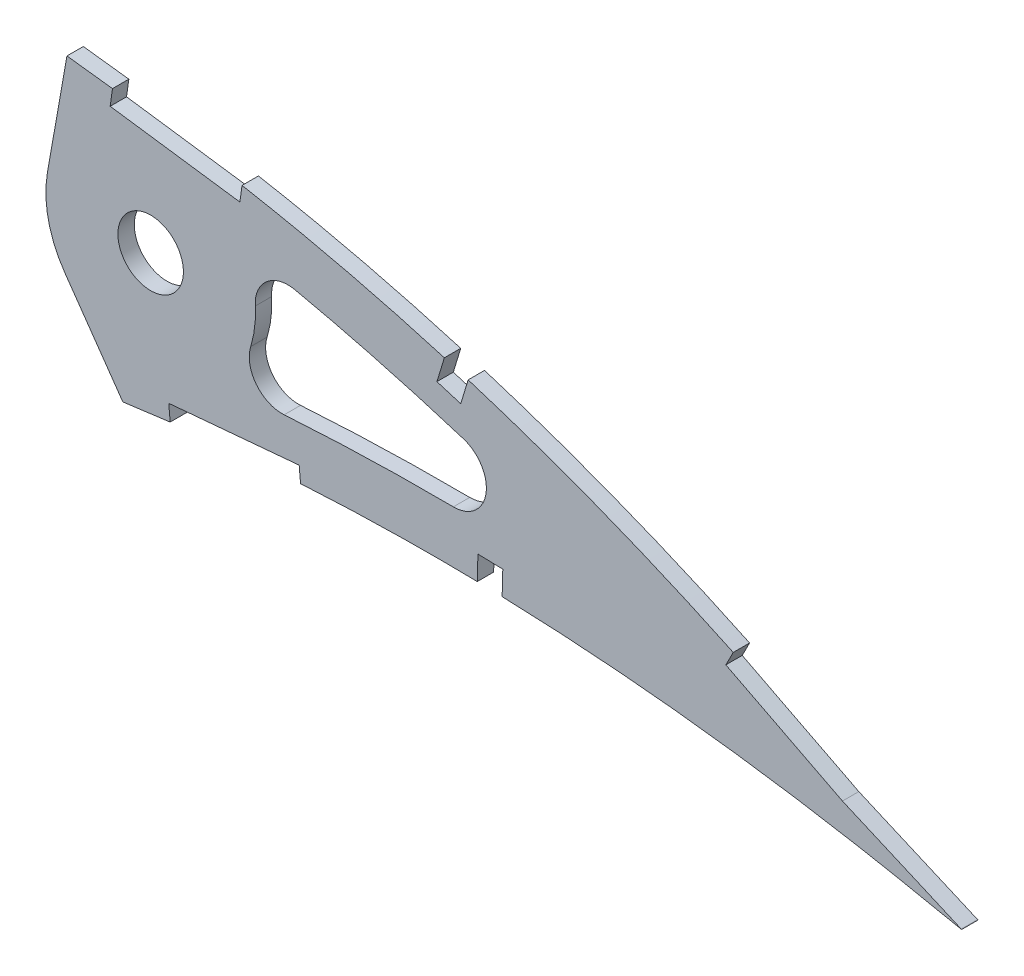
SolidWorks part; units mm, degrees
material "Pine"
ref_plane "Front Plane" through (0, 0, 0) normal (0, 0, 1) x (1, 0, 0)
ref_plane "Top Plane" through (0, 0, 0) normal (0, 1, 0) x (1, 0, 0)
ref_plane "Right Plane" through (0, 0, 0) normal (1, 0, 0) x (0, 0, -1)
curve "Curve2"
  spline degree 3 poles (520.229, 0.8111, 0) (520.1892, 0.8357, 0) (520.0299, 0.9341, 0) (519.6711, 1.1542, 0) (519.0735, 1.5208, 0) (518.237, 2.0313, 0) (517.1622, 2.6844, 0) (515.8486, 3.4756, 0) (514.2969, 4.4021, 0) (512.5075, 5.4598, 0) (510.4807, 6.6436, 0) (508.2172, 7.9486, 0) (505.7172, 9.3676, 0) (502.9816, 10.8948, 0) (500.0114, 12.5227, 0) (496.8072, 14.2443, 0) (493.3701, 16.0505, 0) (489.7015, 17.9338, 0) (485.8019, 19.8836, 0) (481.6733, 21.8919, 0) (477.317, 23.9487, 0) (472.7345, 26.0429, 0) (467.9284, 28.1661, 0) (462.9001, 30.305, 0) (457.6524, 32.4505, 0) (452.1876, 34.5902, 0) (446.5089, 36.7144, 0) (440.6184, 38.8094, 0) (434.5207, 40.866, 0) (428.2186, 42.8708, 0) (421.7166, 44.813, 0) (415.0186, 46.68, 0) (408.1302, 48.4622, 0) (401.0555, 50.1466, 0) (393.8008, 51.7219, 0) (386.3718, 53.1787, 0) (378.7746, 54.5024, 0) (371.0303, 55.692, 0) (363.2636, 56.6815, 0) (355.5128, 57.652, 0) (347.7736, 58.5637, 0) (339.9398, 59.4368, 0) (332.019, 60.2663, 0) (324.019, 61.0497, 0) (315.9478, 61.7836, 0) (307.814, 62.4658, 0) (299.6253, 63.0925, 0) (291.3904, 63.6628, 0) (283.1174, 64.1714, 0) (274.8152, 64.6183, 0) (266.4922, 65.0001, 0) (258.157, 65.3142, 0) (249.8185, 65.5589, 0) (241.4854, 65.7316, 0) (233.1666, 65.8314, 0) (224.8708, 65.8555, 0) (216.6071, 65.8035, 0) (208.384, 65.6736, 0) (200.2107, 65.464, 0) (192.0958, 65.1743, 0) (184.048, 64.8046, 0) (176.0762, 64.3519, 0) (168.189, 63.8191, 0) (160.3952, 63.2038, 0) (152.7034, 62.506, 0) (145.1216, 61.7286, 0) (137.6583, 60.8693, 0) (130.3214, 59.9308, 0) (123.1191, 58.9147, 0) (116.0593, 57.8206, 0) (109.1496, 56.6517, 0) (102.3976, 55.409, 0) (95.8102, 54.0963, 0) (89.3948, 52.714, 0) (83.1581, 51.266, 0) (77.1065, 49.7551, 0) (71.2467, 48.1838, 0) (65.5845, 46.5561, 0) (60.1256, 44.8756, 0) (54.8764, 43.1442, 0) (49.8409, 41.3683, 0) (45.0253, 39.5493, 0) (40.4333, 37.6928, 0) (36.0702, 35.8014, 0) (31.9393, 33.8806, 0) (28.0452, 31.9329, 0) (24.3908, 29.9636, 0) (20.9797, 27.9757, 0) (17.8153, 25.973, 0) (14.8987, 23.9604, 0) (12.2341, 21.9394, 0) (9.8224, 19.9149, 0) (7.6651, 17.8901, 0) (5.7652, 15.8664, 0) (4.1228, 13.8473, 0) (2.7399, 11.8344, 0) (1.6168, 9.8297, 0) (0.7561, 7.8345, 0) (0.1568, 5.85, 0) (-0.1712, 3.8792, 0) (-0.2528, 1.9205, 0) (-0.0842, 0.6392, 0) (0, 0, 0) knots 0 0 0 0 0.000254 0.001015 0.002283 0.004057 0.006331 0.009105 0.012374 0.016134 0.02038 0.025106 0.030306 0.035972 0.0421 0.048678 0.055702 0.06316 0.071046 0.07935 0.088063 0.097176 0.106678 0.116562 0.126814 0.137428 0.148394 0.1597 0.171338 0.183298 0.19557 0.208144 0.221012 0.234162 0.247587 0.261277 0.275223 0.289414 0.303771 0.317689 0.331784 0.34604 0.360444 0.374983 0.38964 0.404403 0.419257 0.434187 0.449177 0.464215 0.479284 0.49437 0.509458 0.524532 0.539579 0.554583 0.56953 0.584403 0.599191 0.613877 0.628447 0.642889 0.657186 0.671326 0.685294 0.699078 0.712665 0.726043 0.739198 0.752118 0.764792 0.777208 0.789356 0.801224 0.812804 0.824083 0.835055 0.84571 0.856038 0.866034 0.875689 0.884998 0.893953 0.902553 0.910789 0.918661 0.926166 0.933303 0.940071 0.946475 0.952518 0.958205 0.963547 0.968557 0.97325 0.977651 0.981787 0.985694 0.989415 0.993001 0.996508 1 1 1 1
curve "Curve3"
  spline degree 3 poles (0, 0, 0) (0.1336, -0.6306, 0) (0.4014, -1.8948, 0) (1.129, -3.7148, 0) (2.0912, -5.4642, 0) (3.3081, -7.1386, 0) (4.7718, -8.7374, 0) (6.479, -10.2623, 0) (8.428, -11.7125, 0) (10.6162, -13.0874, 0) (13.0406, -14.3883, 0) (15.6982, -15.6145, 0) (18.5868, -16.7656, 0) (21.7032, -17.8401, 0) (25.0435, -18.8396, 0) (28.6046, -19.7616, 0) (32.3825, -20.6074, 0) (36.3735, -21.375, 0) (40.5732, -22.065, 0) (44.9774, -22.6771, 0) (49.5814, -23.2117, 0) (54.3808, -23.6676, 0) (59.3708, -24.0458, 0) (64.5464, -24.3466, 0) (69.9027, -24.5709, 0) (75.4344, -24.718, 0) (81.1363, -24.7899, 0) (87.003, -24.788, 0) (93.0289, -24.7115, 0) (99.2088, -24.5648, 0) (105.5368, -24.3469, 0) (112.0073, -24.0604, 0) (118.6142, -23.7083, 0) (125.3518, -23.2917, 0) (132.2141, -22.8125, 0) (139.1951, -22.2745, 0) (146.2885, -21.679, 0) (153.4882, -21.0296, 0) (160.7876, -20.3295, 0) (168.1806, -19.5808, 0) (175.6606, -18.7872, 0) (183.2209, -17.9512, 0) (190.8551, -17.0772, 0) (198.5563, -16.1668, 0) (206.3179, -15.2253, 0) (214.1326, -14.2544, 0) (221.9939, -13.2579, 0) (229.8947, -12.2404, 0) (237.8276, -11.2019, 0) (245.786, -10.1497, 0) (253.7621, -9.0829, 0) (261.7491, -8.0072, 0) (269.7395, -6.9257, 0) (277.7256, -5.8389, 0) (285.7003, -4.7513, 0) (293.6562, -3.6657, 0) (301.5856, -2.5824, 0) (309.4812, -1.5067, 0) (317.3352, -0.4385, 0) (325.1402, 0.6201, 0) (332.8888, 1.6659, 0) (340.5737, 2.6975, 0) (348.187, 3.7144, 0) (355.721, 4.7168, 0) (363.0553, 5.6745, 0) (370.1707, 6.6383, 0) (377.0913, 7.4284, 0) (383.9258, 8.1028, 0) (390.6811, 8.6557, 0) (397.3493, 9.0951, 0) (403.9227, 9.4241, 0) (410.3934, 9.6473, 0) (416.7532, 9.7713, 0) (422.9943, 9.7993, 0) (429.1081, 9.7402, 0) (435.0867, 9.5987, 0) (440.9216, 9.3813, 0) (446.6049, 9.0952, 0) (452.1283, 8.7483, 0) (457.4837, 8.3456, 0) (462.6634, 7.8966, 0) (467.6597, 7.4078, 0) (472.4647, 6.8849, 0) (477.0715, 6.3387, 0) (481.4727, 5.7729, 0) (485.6616, 5.1968, 0) (489.6316, 4.6162, 0) (493.3764, 4.0385, 0) (496.89, 3.4693, 0) (500.1667, 2.916, 0) (503.2016, 2.384, 0) (505.9892, 1.8782, 0) (508.5257, 1.4052, 0) (510.8062, 0.9673, 0) (512.8275, 0.5717, 0) (514.5859, 0.2202, 0) (516.0789, -0.0824, 0) (517.3037, -0.3347, 0) (518.2586, -0.5328, 0) (518.9417, -0.6767, 0) (519.3522, -0.7624, 0) (519.5346, -0.8013, 0) (519.5802, -0.8111, 0) knots 0 0 0 0 0.003638 0.007293 0.011028 0.014901 0.018963 0.023258 0.027821 0.032679 0.037853 0.043362 0.049215 0.055422 0.061989 0.068918 0.076211 0.083868 0.091887 0.100266 0.109 0.118085 0.127515 0.137285 0.147388 0.157816 0.168563 0.179619 0.190977 0.202627 0.21456 0.226767 0.239236 0.251959 0.264924 0.27812 0.291536 0.30516 0.318981 0.332985 0.347163 0.361499 0.375981 0.390597 0.405333 0.420175 0.43511 0.450124 0.465203 0.480333 0.495501 0.51069 0.525887 0.541078 0.556247 0.571382 0.586466 0.601485 0.616424 0.631269 0.646007 0.660621 0.675098 0.689423 0.703582 0.716908 0.730009 0.742952 0.755726 0.76832 0.780724 0.792927 0.804916 0.816679 0.828204 0.839475 0.850481 0.861208 0.871639 0.881763 0.891564 0.901027 0.910139 0.918884 0.927249 0.935221 0.942785 0.949928 0.956638 0.962904 0.968712 0.974054 0.978918 0.983297 0.98718 0.990561 0.993433 0.995791 0.99763 0.998946 0.999737 1 1 1 1
sketch "Sketch1" plane through (0, 0, 0) normal (0, 0, 1) x (1, 0, 0)
  line L1 (519.5802, -0.8111) -> (524.4049, -1.7687)
  line L2 (520.229, 0.8111) -> (524.4049, -1.7687)
  spline S0 degree 3 poles (-2903.7635, -749.124) (66.2436, 68.8235) (-8.6937, 20.855) (1.129, -3.7148) (2.0912, -5.4642) (3.3081, -7.1386) (4.7718, -8.7374) (6.479, -10.2623) (8.428, -11.7125) (10.6162, -13.0874) (13.0406, -14.3883) (15.6982, -15.6145) (18.5868, -16.7656) (21.7032, -17.8401) (25.0435, -18.8396) (28.6046, -19.7616) (32.3825, -20.6074) (36.3735, -21.375) (40.5732, -22.065) (44.9774, -22.6771) (49.5814, -23.2117) (54.3808, -23.6676) (59.3708, -24.0458) (64.5464, -24.3466) (69.9027, -24.5709) (75.4344, -24.718) (81.1363, -24.7899) (87.003, -24.788) (93.0289, -24.7115) (99.2088, -24.5648) (105.5368, -24.3469) (112.0073, -24.0604) (118.6142, -23.7083) (125.3518, -23.2917) (132.2141, -22.8125) (139.1951, -22.2745) (146.2885, -21.679) (153.4882, -21.0296) (160.7876, -20.3295) (168.1806, -19.5808) (175.6606, -18.7872) (183.2209, -17.9512) (190.8551, -17.0772) (198.5563, -16.1668) (206.3179, -15.2253) (214.1326, -14.2544) (221.9939, -13.2579) (229.8947, -12.2404) (237.8276, -11.2019) (245.786, -10.1497) (253.7621, -9.0829) (261.7491, -8.0072) (269.7395, -6.9257) (277.7256, -5.8389) (285.7003, -4.7513) (293.6562, -3.6657) (301.5856, -2.5824) (309.4812, -1.5067) (317.3352, -0.4385) (325.1402, 0.6201) (332.8888, 1.6659) (340.5737, 2.6975) (348.187, 3.7144) (355.721, 4.7168) (363.0553, 5.6745) (370.1707, 6.6383) (377.0913, 7.4284) (383.9258, 8.1028) (390.6811, 8.6557) (397.3493, 9.0951) (403.9227, 9.4241) (410.3934, 9.6473) (416.7532, 9.7713) (422.9943, 9.7993) (429.1081, 9.7402) (435.0867, 9.5987) (440.9216, 9.3813) (446.6049, 9.0952) (452.1283, 8.7483) (457.4837, 8.3456) (462.6634, 7.8966) (467.6597, 7.4078) (472.4647, 6.8849) (477.0715, 6.3387) (481.4727, 5.7729) (485.6616, 5.1968) (489.6316, 4.6162) (493.3764, 4.0385) (496.89, 3.4693) (500.1667, 2.916) (503.2016, 2.384) (505.9892, 1.8782) (508.5257, 1.4052) (510.8062, 0.9673) (512.8275, 0.5717) (514.5859, 0.2202) (516.0789, -0.0824) (517.3037, -0.3347) (518.2586, -0.5328) (518.9417, -0.6767) (537.0698, -4.4604) (553.3394, -15.9066) (1193.1482, 2921.6684) knots -0.137857 -0.137857 -0.137857 -0.137857 0.003638 0.007293 0.011028 0.014901 0.018963 0.023258 0.027821 0.032679 0.037853 0.043362 0.049215 0.055422 0.061989 0.068918 0.076211 0.083868 0.091887 0.100266 0.109 0.118085 0.127515 0.137285 0.147388 0.157816 0.168563 0.179619 0.190977 0.202627 0.21456 0.226767 0.239236 0.251959 0.264924 0.27812 0.291536 0.30516 0.318981 0.332985 0.347163 0.361499 0.375981 0.390597 0.405333 0.420175 0.43511 0.450124 0.465203 0.480333 0.495501 0.51069 0.525887 0.541078 0.556247 0.571382 0.586466 0.601485 0.616424 0.631269 0.646007 0.660621 0.675098 0.689423 0.703582 0.716908 0.730009 0.742952 0.755726 0.76832 0.780724 0.792927 0.804916 0.816679 0.828204 0.839475 0.850481 0.861208 0.871639 0.881763 0.891564 0.901027 0.910139 0.918884 0.927249 0.935221 0.942785 0.949928 0.956638 0.962904 0.968712 0.974054 0.978918 0.983297 0.98718 0.990561 0.993433 0.995791 0.99763 0.998946 0.999737 1.102307 1.102307 1.102307 1.102307 only from (0, 0) to (519.5802, -0.8111) construction
  spline S1 degree 3 poles (2144.5607, 2521.6799) (550.9976, -26.3511) (537.2872, -9.6513) (519.6711, 1.1542) (519.0735, 1.5208) (518.237, 2.0313) (517.1622, 2.6844) (515.8486, 3.4756) (514.2969, 4.4021) (512.5075, 5.4598) (510.4807, 6.6436) (508.2172, 7.9486) (505.7172, 9.3676) (502.9816, 10.8948) (500.0114, 12.5227) (496.8072, 14.2443) (493.3701, 16.0505) (489.7015, 17.9338) (485.8019, 19.8836) (481.6733, 21.8919) (477.317, 23.9487) (472.7345, 26.0429) (467.9284, 28.1661) (462.9001, 30.305) (457.6524, 32.4505) (452.1876, 34.5902) (446.5089, 36.7144) (440.6184, 38.8094) (434.5207, 40.866) (428.2186, 42.8708) (421.7166, 44.813) (415.0186, 46.68) (408.1302, 48.4622) (401.0555, 50.1466) (393.8008, 51.7219) (386.3718, 53.1787) (378.7746, 54.5024) (371.0303, 55.692) (363.2636, 56.6815) (355.5128, 57.652) (347.7736, 58.5637) (339.9398, 59.4368) (332.019, 60.2663) (324.019, 61.0497) (315.9478, 61.7836) (307.814, 62.4658) (299.6253, 63.0925) (291.3904, 63.6628) (283.1174, 64.1714) (274.8152, 64.6183) (266.4922, 65.0001) (258.157, 65.3142) (249.8185, 65.5589) (241.4854, 65.7316) (233.1666, 65.8314) (224.8708, 65.8555) (216.6071, 65.8035) (208.384, 65.6736) (200.2107, 65.464) (192.0958, 65.1743) (184.048, 64.8046) (176.0762, 64.3519) (168.189, 63.8191) (160.3952, 63.2038) (152.7034, 62.506) (145.1216, 61.7286) (137.6583, 60.8693) (130.3214, 59.9308) (123.1191, 58.9147) (116.0593, 57.8206) (109.1496, 56.6517) (102.3976, 55.409) (95.8102, 54.0963) (89.3948, 52.714) (83.1581, 51.266) (77.1065, 49.7551) (71.2467, 48.1838) (65.5845, 46.5561) (60.1256, 44.8756) (54.8764, 43.1442) (49.8409, 41.3683) (45.0253, 39.5493) (40.4333, 37.6928) (36.0702, 35.8014) (31.9393, 33.8806) (28.0452, 31.9329) (24.3908, 29.9636) (20.9797, 27.9757) (17.8153, 25.973) (14.8987, 23.9604) (12.2341, 21.9394) (9.8224, 19.9149) (7.6651, 17.8901) (5.7652, 15.8664) (4.1228, 13.8473) (2.7399, 11.8344) (1.6168, 9.8297) (0.7561, 7.8345) (0.1568, 5.85) (-0.1712, 3.8792) (-1.2714, -22.5145) (85.5395, -42.7616) (-2987.8188, -259.5241) knots -0.109813 -0.109813 -0.109813 -0.109813 0.000254 0.001015 0.002283 0.004057 0.006331 0.009105 0.012374 0.016134 0.02038 0.025106 0.030306 0.035972 0.0421 0.048678 0.055702 0.06316 0.071046 0.07935 0.088063 0.097176 0.106678 0.116562 0.126814 0.137428 0.148394 0.1597 0.171338 0.183298 0.19557 0.208144 0.221012 0.234162 0.247587 0.261277 0.275223 0.289414 0.303771 0.317689 0.331784 0.34604 0.360444 0.374983 0.38964 0.404403 0.419257 0.434187 0.449177 0.464215 0.479284 0.49437 0.509458 0.524532 0.539579 0.554583 0.56953 0.584403 0.599191 0.613877 0.628447 0.642889 0.657186 0.671326 0.685294 0.699078 0.712665 0.726043 0.739198 0.752118 0.764792 0.777208 0.789356 0.801224 0.812804 0.824083 0.835055 0.84571 0.856038 0.866034 0.875689 0.884998 0.893953 0.902553 0.910789 0.918661 0.926166 0.933303 0.940071 0.946475 0.952518 0.958205 0.963547 0.968557 0.97325 0.977651 0.981787 0.985694 0.989415 0.993001 0.996508 1.132043 1.132043 1.132043 1.132043 only from (520.229, 0.8111) to (0, 0) construction
  spline S2 degree 3 poles (0, 0) (0.1336, -0.6306) (0.4014, -1.8948) (1.129, -3.7148) (2.0912, -5.4642) (3.3081, -7.1386) (4.7718, -8.7374) (6.479, -10.2623) (8.428, -11.7125) (10.6162, -13.0874) (13.0406, -14.3883) (15.6982, -15.6145) (18.5868, -16.7656) (21.7032, -17.8401) (25.0435, -18.8396) (28.6046, -19.7616) (32.3825, -20.6074) (36.3735, -21.375) (40.5732, -22.065) (44.9774, -22.6771) (49.5814, -23.2117) (54.3808, -23.6676) (59.3708, -24.0458) (64.5464, -24.3466) (69.9027, -24.5709) (75.4344, -24.718) (81.1363, -24.7899) (87.003, -24.788) (93.0289, -24.7115) (99.2088, -24.5648) (105.5368, -24.3469) (112.0073, -24.0604) (118.6142, -23.7083) (125.3518, -23.2917) (132.2141, -22.8125) (139.1951, -22.2745) (146.2885, -21.679) (153.4882, -21.0296) (160.7876, -20.3295) (168.1806, -19.5808) (175.6606, -18.7872) (183.2209, -17.9512) (190.8551, -17.0772) (198.5563, -16.1668) (206.3179, -15.2253) (214.1326, -14.2544) (221.9939, -13.2579) (229.8947, -12.2404) (237.8276, -11.2019) (245.786, -10.1497) (253.7621, -9.0829) (261.7491, -8.0072) (269.7395, -6.9257) (277.7256, -5.8389) (285.7003, -4.7513) (293.6562, -3.6657) (301.5856, -2.5824) (309.4812, -1.5067) (317.3352, -0.4385) (325.1402, 0.6201) (332.8888, 1.6659) (340.5737, 2.6975) (348.187, 3.7144) (355.721, 4.7168) (363.0553, 5.6745) (370.1707, 6.6383) (377.0913, 7.4284) (383.9258, 8.1028) (390.6811, 8.6557) (397.3493, 9.0951) (403.9227, 9.4241) (410.3934, 9.6473) (416.7532, 9.7713) (422.9943, 9.7993) (429.1081, 9.7402) (435.0867, 9.5987) (440.9216, 9.3813) (446.6049, 9.0952) (452.1283, 8.7483) (457.4837, 8.3456) (462.6634, 7.8966) (467.6597, 7.4078) (472.4647, 6.8849) (477.0715, 6.3387) (481.4727, 5.7729) (485.6616, 5.1968) (489.6316, 4.6162) (493.3764, 4.0385) (496.89, 3.4693) (500.1667, 2.916) (503.2016, 2.384) (505.9892, 1.8782) (508.5257, 1.4052) (510.8062, 0.9673) (512.8275, 0.5717) (514.5859, 0.2202) (516.0789, -0.0824) (517.3037, -0.3347) (518.2586, -0.5328) (518.9417, -0.6767) (519.3522, -0.7624) (519.5346, -0.8013) (519.5802, -0.8111) knots 0 0 0 0 0.003638 0.007293 0.011028 0.014901 0.018963 0.023258 0.027821 0.032679 0.037853 0.043362 0.049215 0.055422 0.061989 0.068918 0.076211 0.083868 0.091887 0.100266 0.109 0.118085 0.127515 0.137285 0.147388 0.157816 0.168563 0.179619 0.190977 0.202627 0.21456 0.226767 0.239236 0.251959 0.264924 0.27812 0.291536 0.30516 0.318981 0.332985 0.347163 0.361499 0.375981 0.390597 0.405333 0.420175 0.43511 0.450124 0.465203 0.480333 0.495501 0.51069 0.525887 0.541078 0.556247 0.571382 0.586466 0.601485 0.616424 0.631269 0.646007 0.660621 0.675098 0.689423 0.703582 0.716908 0.730009 0.742952 0.755726 0.76832 0.780724 0.792927 0.804916 0.816679 0.828204 0.839475 0.850481 0.861208 0.871639 0.881763 0.891564 0.901027 0.910139 0.918884 0.927249 0.935221 0.942785 0.949928 0.956638 0.962904 0.968712 0.974054 0.978918 0.983297 0.98718 0.990561 0.993433 0.995791 0.99763 0.998946 0.999737 1 1 1 1
  spline S3 degree 3 poles (520.229, 0.8111) (520.1892, 0.8357) (520.0299, 0.9341) (519.6711, 1.1542) (519.0735, 1.5208) (518.237, 2.0313) (517.1622, 2.6844) (515.8486, 3.4756) (514.2969, 4.4021) (512.5075, 5.4598) (510.4807, 6.6436) (508.2172, 7.9486) (505.7172, 9.3676) (502.9816, 10.8948) (500.0114, 12.5227) (496.8072, 14.2443) (493.3701, 16.0505) (489.7015, 17.9338) (485.8019, 19.8836) (481.6733, 21.8919) (477.317, 23.9487) (472.7345, 26.0429) (467.9284, 28.1661) (462.9001, 30.305) (457.6524, 32.4505) (452.1876, 34.5902) (446.5089, 36.7144) (440.6184, 38.8094) (434.5207, 40.866) (428.2186, 42.8708) (421.7166, 44.813) (415.0186, 46.68) (408.1302, 48.4622) (401.0555, 50.1466) (393.8008, 51.7219) (386.3718, 53.1787) (378.7746, 54.5024) (371.0303, 55.692) (363.2636, 56.6815) (355.5128, 57.652) (347.7736, 58.5637) (339.9398, 59.4368) (332.019, 60.2663) (324.019, 61.0497) (315.9478, 61.7836) (307.814, 62.4658) (299.6253, 63.0925) (291.3904, 63.6628) (283.1174, 64.1714) (274.8152, 64.6183) (266.4922, 65.0001) (258.157, 65.3142) (249.8185, 65.5589) (241.4854, 65.7316) (233.1666, 65.8314) (224.8708, 65.8555) (216.6071, 65.8035) (208.384, 65.6736) (200.2107, 65.464) (192.0958, 65.1743) (184.048, 64.8046) (176.0762, 64.3519) (168.189, 63.8191) (160.3952, 63.2038) (152.7034, 62.506) (145.1216, 61.7286) (137.6583, 60.8693) (130.3214, 59.9308) (123.1191, 58.9147) (116.0593, 57.8206) (109.1496, 56.6517) (102.3976, 55.409) (95.8102, 54.0963) (89.3948, 52.714) (83.1581, 51.266) (77.1065, 49.7551) (71.2467, 48.1838) (65.5845, 46.5561) (60.1256, 44.8756) (54.8764, 43.1442) (49.8409, 41.3683) (45.0253, 39.5493) (40.4333, 37.6928) (36.0702, 35.8014) (31.9393, 33.8806) (28.0452, 31.9329) (24.3908, 29.9636) (20.9797, 27.9757) (17.8153, 25.973) (14.8987, 23.9604) (12.2341, 21.9394) (9.8224, 19.9149) (7.6651, 17.8901) (5.7652, 15.8664) (4.1228, 13.8473) (2.7399, 11.8344) (1.6168, 9.8297) (0.7561, 7.8345) (0.1568, 5.85) (-0.1712, 3.8792) (-0.2528, 1.9205) (-0.0842, 0.6392) (0, 0) knots 0 0 0 0 0.000254 0.001015 0.002283 0.004057 0.006331 0.009105 0.012374 0.016134 0.02038 0.025106 0.030306 0.035972 0.0421 0.048678 0.055702 0.06316 0.071046 0.07935 0.088063 0.097176 0.106678 0.116562 0.126814 0.137428 0.148394 0.1597 0.171338 0.183298 0.19557 0.208144 0.221012 0.234162 0.247587 0.261277 0.275223 0.289414 0.303771 0.317689 0.331784 0.34604 0.360444 0.374983 0.38964 0.404403 0.419257 0.434187 0.449177 0.464215 0.479284 0.49437 0.509458 0.524532 0.539579 0.554583 0.56953 0.584403 0.599191 0.613877 0.628447 0.642889 0.657186 0.671326 0.685294 0.699078 0.712665 0.726043 0.739198 0.752118 0.764792 0.777208 0.789356 0.801224 0.812804 0.824083 0.835055 0.84571 0.856038 0.866034 0.875689 0.884998 0.893953 0.902553 0.910789 0.918661 0.926166 0.933303 0.940071 0.946475 0.952518 0.958205 0.963547 0.968557 0.97325 0.977651 0.981787 0.985694 0.989415 0.993001 0.996508 1 1 1 1
extrude "Boss-Extrude1" add sketch "Sketch1" along normal blind 3.175
sketch "Sketch4" plane through (0, 0, 0) normal (0, 0, -1) x (-1, 0, 0)
  line L0 (-347.1309, 36.7611) -> (-350.9097, 58.1919)
  line L1 (-350.497, 21.5775) -> (-361.7496, 5.5072)
  line L2 (-367.1422, 33.2326) -> (-406.863, 33.2326)
  circle A0 centre (-367.1422, 33.2326) radius 20.32
  circle A1 centre (-367.1422, 33.2326) radius 6.35
  spline S2 degree 3 poles (1939.7558, -484.7932) (-49.4812, 57.6608) (7.5449, 17.9816) (-1.129, -3.7148) (-2.0912, -5.4642) (-3.3081, -7.1386) (-4.7718, -8.7374) (-6.479, -10.2623) (-8.428, -11.7125) (-10.6162, -13.0874) (-13.0406, -14.3883) (-15.6982, -15.6145) (-18.5868, -16.7656) (-21.7032, -17.8401) (-25.0435, -18.8396) (-28.6046, -19.7616) (-32.3825, -20.6074) (-36.3735, -21.375) (-40.5732, -22.065) (-44.9774, -22.6771) (-49.5814, -23.2117) (-54.3808, -23.6676) (-59.3708, -24.0458) (-64.5464, -24.3466) (-69.9027, -24.5709) (-75.4344, -24.718) (-81.1363, -24.7899) (-87.003, -24.788) (-93.0289, -24.7115) (-99.2088, -24.5648) (-105.5368, -24.3469) (-112.0073, -24.0604) (-118.6142, -23.7083) (-125.3518, -23.2917) (-132.2141, -22.8125) (-139.1951, -22.2745) (-146.2885, -21.679) (-153.4882, -21.0296) (-160.7876, -20.3295) (-168.1806, -19.5808) (-175.6606, -18.7872) (-183.2209, -17.9512) (-190.8551, -17.0772) (-198.5563, -16.1668) (-206.3179, -15.2253) (-214.1326, -14.2544) (-221.9939, -13.2579) (-229.8947, -12.2404) (-237.8276, -11.2019) (-245.786, -10.1497) (-253.7621, -9.0829) (-261.7491, -8.0072) (-269.7395, -6.9257) (-277.7256, -5.8389) (-285.7003, -4.7513) (-293.6562, -3.6657) (-301.5856, -2.5824) (-309.4812, -1.5067) (-317.3352, -0.4385) (-325.1402, 0.6201) (-332.8888, 1.6659) (-340.5737, 2.6975) (-348.187, 3.7144) (-355.721, 4.7168) (-363.0553, 5.6745) (-370.1707, 6.6383) (-377.0913, 7.4284) (-383.9258, 8.1028) (-390.6811, 8.6557) (-397.3493, 9.0951) (-403.9227, 9.4241) (-410.3934, 9.6473) (-416.7532, 9.7713) (-422.9943, 9.7993) (-429.1081, 9.7402) (-435.0867, 9.5987) (-440.9216, 9.3813) (-446.6049, 9.0952) (-452.1283, 8.7483) (-457.4837, 8.3456) (-462.6634, 7.8966) (-467.6597, 7.4078) (-472.4647, 6.8849) (-477.0715, 6.3387) (-481.4727, 5.7729) (-485.6616, 5.1968) (-489.6316, 4.6162) (-493.3764, 4.0385) (-496.89, 3.4693) (-500.1667, 2.916) (-503.2016, 2.384) (-505.9892, 1.8782) (-508.5257, 1.4052) (-510.8062, 0.9673) (-512.8275, 0.5717) (-514.5859, 0.2202) (-516.0789, -0.0824) (-517.3037, -0.3347) (-518.2586, -0.5328) (-518.9417, -0.6767) (-534.8295, -3.9928) (-549.2415, -13.1623) (-979.5797, 1945.0117) knots -0.120445 -0.120445 -0.120445 -0.120445 0.003638 0.007293 0.011028 0.014901 0.018963 0.023258 0.027821 0.032679 0.037853 0.043362 0.049215 0.055422 0.061989 0.068918 0.076211 0.083868 0.091887 0.100266 0.109 0.118085 0.127515 0.137285 0.147388 0.157816 0.168563 0.179619 0.190977 0.202627 0.21456 0.226767 0.239236 0.251959 0.264924 0.27812 0.291536 0.30516 0.318981 0.332985 0.347163 0.361499 0.375981 0.390597 0.405333 0.420175 0.43511 0.450124 0.465203 0.480333 0.495501 0.51069 0.525887 0.541078 0.556247 0.571382 0.586466 0.601485 0.616424 0.631269 0.646007 0.660621 0.675098 0.689423 0.703582 0.716908 0.730009 0.742952 0.755726 0.76832 0.780724 0.792927 0.804916 0.816679 0.828204 0.839475 0.850481 0.861208 0.871639 0.881763 0.891564 0.901027 0.910139 0.918884 0.927249 0.935221 0.942785 0.949928 0.956638 0.962904 0.968712 0.974054 0.978918 0.983297 0.98718 0.990561 0.993433 0.995791 0.99763 0.998946 0.999737 1.089371 1.089371 1.089371 1.089371 only from (0, 0) to (-519.5802, -0.8111) construction
  spline S3 degree 3 poles (-1613.7482, 1674.6901) (-547.5042, -22.2613) (-535.1053, -8.313) (-519.6711, 1.1542) (-519.0735, 1.5208) (-518.237, 2.0313) (-517.1622, 2.6844) (-515.8486, 3.4756) (-514.2969, 4.4021) (-512.5075, 5.4598) (-510.4807, 6.6436) (-508.2172, 7.9486) (-505.7172, 9.3676) (-502.9816, 10.8948) (-500.0114, 12.5227) (-496.8072, 14.2443) (-493.3701, 16.0505) (-489.7015, 17.9338) (-485.8019, 19.8836) (-481.6733, 21.8919) (-477.317, 23.9487) (-472.7345, 26.0429) (-467.9284, 28.1661) (-462.9001, 30.305) (-457.6524, 32.4505) (-452.1876, 34.5902) (-446.5089, 36.7144) (-440.6184, 38.8094) (-434.5207, 40.866) (-428.2186, 42.8708) (-421.7166, 44.813) (-415.0186, 46.68) (-408.1302, 48.4622) (-401.0555, 50.1466) (-393.8008, 51.7219) (-386.3718, 53.1787) (-378.7746, 54.5024) (-371.0303, 55.692) (-363.2636, 56.6815) (-355.5128, 57.652) (-347.7736, 58.5637) (-339.9398, 59.4368) (-332.019, 60.2663) (-324.019, 61.0497) (-315.9478, 61.7836) (-307.814, 62.4658) (-299.6253, 63.0925) (-291.3904, 63.6628) (-283.1174, 64.1714) (-274.8152, 64.6183) (-266.4922, 65.0001) (-258.157, 65.3142) (-249.8185, 65.5589) (-241.4854, 65.7316) (-233.1666, 65.8314) (-224.8708, 65.8555) (-216.6071, 65.8035) (-208.384, 65.6736) (-200.2107, 65.464) (-192.0958, 65.1743) (-184.048, 64.8046) (-176.0762, 64.3519) (-168.189, 63.8191) (-160.3952, 63.2038) (-152.7034, 62.506) (-145.1216, 61.7286) (-137.6583, 60.8693) (-130.3214, 59.9308) (-123.1191, 58.9147) (-116.0593, 57.8206) (-109.1496, 56.6517) (-102.3976, 55.409) (-95.8102, 54.0963) (-89.3948, 52.714) (-83.1581, 51.266) (-77.1065, 49.7551) (-71.2467, 48.1838) (-65.5845, 46.5561) (-60.1256, 44.8756) (-54.8764, 43.1442) (-49.8409, 41.3683) (-45.0253, 39.5493) (-40.4333, 37.6928) (-36.0702, 35.8014) (-31.9393, 33.8806) (-28.0452, 31.9329) (-24.3908, 29.9636) (-20.9797, 27.9757) (-17.8153, 25.973) (-14.8987, 23.9604) (-12.2341, 21.9394) (-9.8224, 19.9149) (-7.6651, 17.8901) (-5.7652, 15.8664) (-4.1228, 13.8473) (-2.7399, 11.8344) (-1.6168, 9.8297) (-0.7561, 7.8345) (-0.1568, 5.85) (0.1712, 3.8792) (1.1427, -19.4272) (-65.9725, -37.8239) (1990.4087, -188.0581) knots -0.095928 -0.095928 -0.095928 -0.095928 0.000254 0.001015 0.002283 0.004057 0.006331 0.009105 0.012374 0.016134 0.02038 0.025106 0.030306 0.035972 0.0421 0.048678 0.055702 0.06316 0.071046 0.07935 0.088063 0.097176 0.106678 0.116562 0.126814 0.137428 0.148394 0.1597 0.171338 0.183298 0.19557 0.208144 0.221012 0.234162 0.247587 0.261277 0.275223 0.289414 0.303771 0.317689 0.331784 0.34604 0.360444 0.374983 0.38964 0.404403 0.419257 0.434187 0.449177 0.464215 0.479284 0.49437 0.509458 0.524532 0.539579 0.554583 0.56953 0.584403 0.599191 0.613877 0.628447 0.642889 0.657186 0.671326 0.685294 0.699078 0.712665 0.726043 0.739198 0.752118 0.764792 0.777208 0.789356 0.801224 0.812804 0.824083 0.835055 0.84571 0.856038 0.866034 0.875689 0.884998 0.893953 0.902553 0.910789 0.918661 0.926166 0.933303 0.940071 0.946475 0.952518 0.958205 0.963547 0.968557 0.97325 0.977651 0.981787 0.985694 0.989415 0.993001 0.996508 1.11536 1.11536 1.11536 1.11536 only from (-520.229, 0.8111) to (0, 0) construction
  spline S4 degree 3 poles (-1978.354, 2157.5892) (159.6529, 858.6126) (-7.0413, 13.2519) (-10.1565, 1.1414) (-10.167, 1.1042) (-10.1763, 1.0725) (-10.1781, 1.0668) (-10.1835, 1.0497) (-10.1867, 1.0399) (-10.2052, 0.985) (-10.2286, 0.9219) (-10.2791, 0.8017) (-10.2985, 0.7574) (-10.3426, 0.661) (-10.3676, 0.6085) (-10.4428, 0.4561) (-10.496, 0.3558) (-10.6081, 0.1584) (-10.6662, 0.0627) (-10.855, -0.2291) (-11.0064, -0.4384) (-11.5378, -1.0936) (-11.9971, -1.5677) (-13.099, -2.5256) (-13.7412, -3.01) (-15.1702, -3.9568) (-15.9588, -4.4208) (-17.636, -5.3094) (-18.5262, -5.7351) (-21.3094, -6.9503) (-23.3073, -7.6749) (-27.467, -8.9758) (-29.6229, -9.5497) (-34.0316, -10.5753) (-36.2795, -11.0252) (-40.839, -11.8243) (-43.1471, -12.1728) (-47.8035, -12.7862) (-50.1501, -13.0508) (-57.2292, -13.7373) (-62.003, -14.0541) (-71.5985, -14.4809) (-76.422, -14.5891) (-83.6816, -14.6324) (-86.1037, -14.6268) (-90.9551, -14.5789) (-93.3856, -14.5371) (-100.6793, -14.3647) (-105.548, -14.1854) (-120.1773, -13.4939) (-129.9476, -12.83) (-149.5009, -11.2301) (-159.287, -10.2936) (-178.863, -8.2392) (-188.6532, -7.1203) (-203.3458, -5.3542) (-208.2424, -4.7511) (-218.0387, -3.5207) (-222.9395, -2.8943) (-232.7359, -1.6243) (-237.6385, -0.9795) (-247.4393, 0.3202) (-252.3404, 0.9774) (-262.147, 2.2986) (-267.05, 2.9625) (-276.8577, 4.2964) (-281.7641, 4.9659) (-291.5768, 6.3047) (-296.4825, 6.9752) (-306.3007, 8.3142) (-311.2087, 8.9822) (-325.9378, 10.9826) (-335.766, 12.3068) (-348.0467, 13.9451) (-350.5039, 14.2725) (-354.1964, 14.7609) (-355.4285, 14.923) (-357.8843, 15.2457) (-359.1092, 15.4066) (-361.5526, 15.7296) (-362.7689, 15.8922) (-365.2348, 16.221) (-366.4798, 16.3859) (-368.3663, 16.6273) (-368.9995, 16.7068) (-371.53, 17.0174) (-373.424, 17.2342) (-377.8329, 17.7104) (-380.3527, 17.9617) (-385.4072, 18.4196) (-387.9354, 18.6255) (-395.5221, 19.1767) (-400.5883, 19.4552) (-408.19, 19.7386) (-410.7237, 19.8108) (-415.7936, 19.9113) (-418.3301, 19.9392) (-425.9339, 19.9566) (-431.0019, 19.8815) (-441.1324, 19.5579) (-446.1907, 19.3102) (-453.7725, 18.8139) (-456.2982, 18.6271) (-775.6257, -7.5609) (-1062.3017, -351.5368) (-2984.1092, -1609.9578) knots -0.216436 -0.216436 -0.216436 -0.216436 0.001953 0.001953 0.00293 0.00293 0.003418 0.003418 0.003906 0.003906 0.005859 0.005859 0.006836 0.006836 0.007813 0.007813 0.009766 0.009766 0.011719 0.011719 0.015625 0.015625 0.023438 0.023438 0.03125 0.03125 0.039063 0.039063 0.046875 0.046875 0.0625 0.0625 0.078125 0.078125 0.09375 0.09375 0.109375 0.109375 0.125 0.125 0.15625 0.15625 0.1875 0.1875 0.203125 0.203125 0.21875 0.21875 0.25 0.25 0.3125 0.3125 0.375 0.375 0.4375 0.4375 0.46875 0.46875 0.5 0.5 0.53125 0.53125 0.5625 0.5625 0.59375 0.59375 0.625 0.625 0.65625 0.65625 0.6875 0.6875 0.75 0.75 0.765625 0.765625 0.773438 0.773438 0.78125 0.78125 0.789063 0.789063 0.796875 0.796875 0.800781 0.800781 0.8125 0.8125 0.828125 0.828125 0.84375 0.84375 0.875 0.875 0.890625 0.890625 0.90625 0.90625 0.9375 0.9375 0.96875 0.96875 0.984375 0.984375 2.947098 2.947098 2.947098 2.947098 only from (-10.022, 1.7185) to (-466.3815, 17.739)
  spline S5 degree 3 poles (-2960.1923, -1647.6146) (-778.0163, -316.2747) (-661.2066, -63.7231) (-457.1185, 21.6971) (-454.7864, 22.6463) (-450.1039, 24.4978) (-447.7524, 25.4007) (-443.0352, 27.1579) (-440.669, 28.0121) (-428.7885, 32.1652) (-419.1573, 35.0991) (-404.5516, 38.8923) (-399.6593, 40.0545) (-392.2853, 41.6432) (-389.8214, 42.1473) (-384.8862, 43.1026) (-382.4148, 43.5535) (-377.456, 44.4051) (-374.9691, 44.8071) (-371.8706, 45.272) (-371.2512, 45.3631) (-370.0129, 45.5414) (-369.3949, 45.6283) (-367.531, 45.885) (-365.6514, 46.1331) (-363.7495, 46.3759) (-362.4766, 46.5374) (-361.8369, 46.6182) (-359.9197, 46.8599) (-358.6437, 47.0199) (-354.8218, 47.4941) (-352.2828, 47.8012) (-347.1922, 48.3982) (-344.6438, 48.6888) (-339.5477, 49.2537) (-336.9993, 49.5279) (-329.3512, 50.3256) (-324.2496, 50.8242) (-308.9368, 52.2174) (-298.7176, 53.0107) (-278.2717, 54.3039) (-268.0406, 54.8057) (-247.5801, 55.4913) (-237.3501, 55.6755) (-216.9004, 55.6922) (-206.6831, 55.5256) (-191.3779, 54.9785) (-186.2812, 54.7472) (-176.0979, 54.177) (-171.0099, 53.8396) (-160.8533, 53.0504) (-155.7814, 52.598) (-145.6574, 51.572) (-140.6072, 50.9971) (-125.4892, 49.071) (-115.4646, 47.5214) (-100.5547, 44.7064) (-95.6096, 43.687) (-85.777, 41.462) (-80.8922, 40.2578) (-71.2072, 37.6367) (-66.4068, 36.2209) (-59.3024, 33.909) (-56.9474, 33.1063) (-52.2821, 31.4343) (-49.9693, 30.5636) (-45.3927, 28.7458) (-43.1318, 27.7996) (-38.6715, 25.8196) (-36.476, 24.7882) (-32.1758, 22.6281) (-30.0692, 21.4995) (-27.0125, 19.7284) (-26.0103, 19.1247) (-24.0464, 17.889) (-23.0831, 17.2561) (-21.2128, 15.9659) (-20.3049, 15.3076) (-18.5534, 13.9629) (-17.7093, 13.2763) (-16.1081, 11.8824) (-15.3519, 11.176) (-14.3045, 10.1109) (-13.9701, 9.7552) (-13.3325, 9.0431) (-13.0296, 8.687) (-12.1803, 7.6299) (-11.6896, 6.9348) (-10.8906, 5.6128) (-10.5874, 4.9936) (-10.269, 4.158) (-10.1861, 3.8969) (-10.0953, 3.5459) (-10.0707, 3.4366) (-10.0267, 3.2104) (-10.0081, 3.096) (-9.9777, 2.8649) (-9.9658, 2.7438) (-9.9529, 2.5547) (-9.9512, 2.4811) (-9.9516, 2.4178) (-9.9518, 2.4066) (-9.9523, 2.387) (-9.9526, 2.38) (-9.9538, 2.3538) (-9.956, 2.318) (-10.9137, -8.9231) (-124.2495, -805.3826) (-2616.8841, -1329.8892) knots -1.341255 -1.341255 -1.341255 -1.341255 0.015625 0.015625 0.03125 0.03125 0.046875 0.046875 0.0625 0.0625 0.125 0.125 0.15625 0.15625 0.171875 0.171875 0.1875 0.1875 0.203125 0.203125 0.207031 0.207031 0.210937 0.210937 0.21875 0.222656 0.222656 0.226562 0.226562 0.234375 0.234375 0.25 0.25 0.265625 0.265625 0.28125 0.28125 0.3125 0.3125 0.375 0.375 0.4375 0.4375 0.5 0.5 0.5625 0.5625 0.59375 0.59375 0.625 0.625 0.65625 0.65625 0.6875 0.6875 0.75 0.75 0.78125 0.78125 0.8125 0.8125 0.84375 0.84375 0.859375 0.859375 0.875 0.875 0.890625 0.890625 0.90625 0.90625 0.921875 0.921875 0.929688 0.929688 0.9375 0.9375 0.945313 0.945313 0.953125 0.953125 0.960938 0.960938 0.964844 0.964844 0.96875 0.96875 0.976563 0.976563 0.984375 0.984375 0.988281 0.988281 0.990234 0.990234 0.992188 0.992188 0.994141 0.994141 0.996094 0.996094 0.996582 0.996582 0.99707 0.99707 0.998047 0.998047 1.199641 1.199641 1.199641 1.199641 only from (-466.3815, 17.739) to (-10.022, 1.7185)
  spline S6 degree 3 poles (-10.022, 1.7185) (-10.0741, 1.4777) (-10.1149, 1.3032) (-10.1565, 1.1414) (-10.167, 1.1042) (-10.1763, 1.0725) (-10.1781, 1.0668) (-10.1835, 1.0497) (-10.1867, 1.0399) (-10.2052, 0.985) (-10.2286, 0.9219) (-10.2791, 0.8017) (-10.2985, 0.7574) (-10.3426, 0.661) (-10.3676, 0.6085) (-10.4428, 0.4561) (-10.496, 0.3558) (-10.6081, 0.1584) (-10.6662, 0.0627) (-10.855, -0.2291) (-11.0064, -0.4384) (-11.5378, -1.0936) (-11.9971, -1.5677) (-13.099, -2.5256) (-13.7412, -3.01) (-15.1702, -3.9568) (-15.9588, -4.4208) (-17.636, -5.3094) (-18.5262, -5.7351) (-21.3094, -6.9503) (-23.3073, -7.6749) (-27.467, -8.9758) (-29.6229, -9.5497) (-34.0316, -10.5753) (-36.2795, -11.0252) (-40.839, -11.8243) (-43.1471, -12.1728) (-47.8035, -12.7862) (-50.1501, -13.0508) (-57.2292, -13.7373) (-62.003, -14.0541) (-71.5985, -14.4809) (-76.422, -14.5891) (-83.6816, -14.6324) (-86.1037, -14.6268) (-90.9551, -14.5789) (-93.3856, -14.5371) (-100.6793, -14.3647) (-105.548, -14.1854) (-120.1773, -13.4939) (-129.9476, -12.83) (-149.5009, -11.2301) (-159.287, -10.2936) (-178.863, -8.2392) (-188.6532, -7.1203) (-203.3458, -5.3542) (-208.2424, -4.7511) (-218.0387, -3.5207) (-222.9395, -2.8943) (-232.7359, -1.6243) (-237.6385, -0.9795) (-247.4393, 0.3202) (-252.3404, 0.9774) (-262.147, 2.2986) (-267.05, 2.9625) (-276.8577, 4.2964) (-281.7641, 4.9659) (-291.5768, 6.3047) (-296.4825, 6.9752) (-306.3007, 8.3142) (-311.2087, 8.9822) (-325.9378, 10.9826) (-335.766, 12.3068) (-348.0467, 13.9451) (-350.5039, 14.2725) (-354.1964, 14.7609) (-355.4285, 14.923) (-357.8843, 15.2457) (-359.1092, 15.4066) (-361.5526, 15.7296) (-362.7689, 15.8922) (-365.2348, 16.221) (-366.4798, 16.3859) (-368.3663, 16.6273) (-368.9995, 16.7068) (-371.53, 17.0174) (-373.424, 17.2342) (-377.8329, 17.7104) (-380.3527, 17.9617) (-385.4072, 18.4196) (-387.9354, 18.6255) (-395.5221, 19.1767) (-400.5883, 19.4552) (-408.19, 19.7386) (-410.7237, 19.8108) (-415.7936, 19.9113) (-418.3301, 19.9392) (-425.9339, 19.9566) (-431.0019, 19.8815) (-441.1324, 19.5579) (-446.1907, 19.3102) (-453.7725, 18.8139) (-456.2982, 18.6271) (-461.3423, 18.2134) (-463.8625, 17.9865) (-466.3815, 17.739) knots 0 0 0 0 0.001953 0.001953 0.00293 0.00293 0.003418 0.003418 0.003906 0.003906 0.005859 0.005859 0.006836 0.006836 0.007813 0.007813 0.009766 0.009766 0.011719 0.011719 0.015625 0.015625 0.023438 0.023438 0.03125 0.03125 0.039063 0.039063 0.046875 0.046875 0.0625 0.0625 0.078125 0.078125 0.09375 0.09375 0.109375 0.109375 0.125 0.125 0.15625 0.15625 0.1875 0.1875 0.203125 0.203125 0.21875 0.21875 0.25 0.25 0.3125 0.3125 0.375 0.375 0.4375 0.4375 0.46875 0.46875 0.5 0.5 0.53125 0.53125 0.5625 0.5625 0.59375 0.59375 0.625 0.625 0.65625 0.65625 0.6875 0.6875 0.75 0.75 0.765625 0.765625 0.773438 0.773438 0.78125 0.78125 0.789063 0.789063 0.796875 0.796875 0.800781 0.800781 0.8125 0.8125 0.828125 0.828125 0.84375 0.84375 0.875 0.875 0.890625 0.890625 0.90625 0.90625 0.9375 0.9375 0.96875 0.96875 0.984375 0.984375 1 1 1 1
  spline S7 degree 3 poles (-466.3815, 17.739) (-464.0774, 18.7574) (-461.7652, 19.7522) (-457.1185, 21.6971) (-454.7864, 22.6463) (-450.1039, 24.4978) (-447.7524, 25.4007) (-443.0352, 27.1579) (-440.669, 28.0121) (-428.7885, 32.1652) (-419.1573, 35.0991) (-404.5516, 38.8923) (-399.6593, 40.0545) (-392.2853, 41.6432) (-389.8214, 42.1473) (-384.8862, 43.1026) (-382.4148, 43.5535) (-377.456, 44.4051) (-374.9691, 44.8071) (-371.8706, 45.272) (-371.2512, 45.3631) (-370.0129, 45.5414) (-369.3949, 45.6283) (-367.531, 45.885) (-365.6514, 46.1331) (-363.7495, 46.3759) (-362.4766, 46.5374) (-361.8369, 46.6182) (-359.9197, 46.8599) (-358.6437, 47.0199) (-354.8218, 47.4941) (-352.2828, 47.8012) (-347.1922, 48.3982) (-344.6438, 48.6888) (-339.5477, 49.2537) (-336.9993, 49.5279) (-329.3512, 50.3256) (-324.2496, 50.8242) (-308.9368, 52.2174) (-298.7176, 53.0107) (-278.2717, 54.3039) (-268.0406, 54.8057) (-247.5801, 55.4913) (-237.3501, 55.6755) (-216.9004, 55.6922) (-206.6831, 55.5256) (-191.3779, 54.9785) (-186.2812, 54.7472) (-176.0979, 54.177) (-171.0099, 53.8396) (-160.8533, 53.0504) (-155.7814, 52.598) (-145.6574, 51.572) (-140.6072, 50.9971) (-125.4892, 49.071) (-115.4646, 47.5214) (-100.5547, 44.7064) (-95.6096, 43.687) (-85.777, 41.462) (-80.8922, 40.2578) (-71.2072, 37.6367) (-66.4068, 36.2209) (-59.3024, 33.909) (-56.9474, 33.1063) (-52.2821, 31.4343) (-49.9693, 30.5636) (-45.3927, 28.7458) (-43.1318, 27.7996) (-38.6715, 25.8196) (-36.476, 24.7882) (-32.1758, 22.6281) (-30.0692, 21.4995) (-27.0125, 19.7284) (-26.0103, 19.1247) (-24.0464, 17.889) (-23.0831, 17.2561) (-21.2128, 15.9659) (-20.3049, 15.3076) (-18.5534, 13.9629) (-17.7093, 13.2763) (-16.1081, 11.8824) (-15.3519, 11.176) (-14.3045, 10.1109) (-13.9701, 9.7552) (-13.3325, 9.0431) (-13.0296, 8.687) (-12.1803, 7.6299) (-11.6896, 6.9348) (-10.8906, 5.6128) (-10.5874, 4.9936) (-10.269, 4.158) (-10.1861, 3.8969) (-10.0953, 3.5459) (-10.0707, 3.4366) (-10.0267, 3.2104) (-10.0081, 3.096) (-9.9777, 2.8649) (-9.9658, 2.7438) (-9.9529, 2.5547) (-9.9512, 2.4811) (-9.9516, 2.4178) (-9.9518, 2.4066) (-9.9523, 2.387) (-9.9526, 2.38) (-9.9538, 2.3538) (-9.956, 2.318) (-9.9698, 2.1554) (-9.9896, 1.9733) (-10.022, 1.7185) knots 0 0 0 0 0.015625 0.015625 0.03125 0.03125 0.046875 0.046875 0.0625 0.0625 0.125 0.125 0.15625 0.15625 0.171875 0.171875 0.1875 0.1875 0.203125 0.203125 0.207031 0.207031 0.210937 0.210937 0.21875 0.222656 0.222656 0.226562 0.226562 0.234375 0.234375 0.25 0.25 0.265625 0.265625 0.28125 0.28125 0.3125 0.3125 0.375 0.375 0.4375 0.4375 0.5 0.5 0.5625 0.5625 0.59375 0.59375 0.625 0.625 0.65625 0.65625 0.6875 0.6875 0.75 0.75 0.78125 0.78125 0.8125 0.8125 0.84375 0.84375 0.859375 0.859375 0.875 0.875 0.890625 0.890625 0.90625 0.90625 0.921875 0.921875 0.929688 0.929688 0.9375 0.9375 0.945313 0.945313 0.953125 0.953125 0.960938 0.960938 0.964844 0.964844 0.96875 0.96875 0.976563 0.976563 0.984375 0.984375 0.988281 0.988281 0.990234 0.990234 0.992188 0.992188 0.994141 0.994141 0.996094 0.996094 0.996582 0.996582 0.99707 0.99707 0.998047 0.998047 1 1 1 1
  spline S8 degree 3 poles (0, 0) (-0.1336, -0.6306) (-0.4014, -1.8948) (-1.129, -3.7148) (-2.0912, -5.4642) (-3.3081, -7.1386) (-4.7718, -8.7374) (-6.479, -10.2623) (-8.428, -11.7125) (-10.6162, -13.0874) (-13.0406, -14.3883) (-15.6982, -15.6145) (-18.5868, -16.7656) (-21.7032, -17.8401) (-25.0435, -18.8396) (-28.6046, -19.7616) (-32.3825, -20.6074) (-36.3735, -21.375) (-40.5732, -22.065) (-44.9774, -22.6771) (-49.5814, -23.2117) (-54.3808, -23.6676) (-59.3708, -24.0458) (-64.5464, -24.3466) (-69.9027, -24.5709) (-75.4344, -24.718) (-81.1363, -24.7899) (-87.003, -24.788) (-93.0289, -24.7115) (-99.2088, -24.5648) (-105.5368, -24.3469) (-112.0073, -24.0604) (-118.6142, -23.7083) (-125.3518, -23.2917) (-132.2141, -22.8125) (-139.1951, -22.2745) (-146.2885, -21.679) (-153.4882, -21.0296) (-160.7876, -20.3295) (-168.1806, -19.5808) (-175.6606, -18.7872) (-183.2209, -17.9512) (-190.8551, -17.0772) (-198.5563, -16.1668) (-206.3179, -15.2253) (-214.1326, -14.2544) (-221.9939, -13.2579) (-229.8947, -12.2404) (-237.8276, -11.2019) (-245.786, -10.1497) (-253.7621, -9.0829) (-261.7491, -8.0072) (-269.7395, -6.9257) (-277.7256, -5.8389) (-285.7003, -4.7513) (-293.6562, -3.6657) (-301.5856, -2.5824) (-309.4812, -1.5067) (-317.3352, -0.4385) (-325.1402, 0.6201) (-332.8888, 1.6659) (-340.5737, 2.6975) (-348.187, 3.7144) (-355.721, 4.7168) (-363.0553, 5.6745) (-370.1707, 6.6383) (-377.0913, 7.4284) (-383.9258, 8.1028) (-390.6811, 8.6557) (-397.3493, 9.0951) (-403.9227, 9.4241) (-410.3934, 9.6473) (-416.7532, 9.7713) (-422.9943, 9.7993) (-429.1081, 9.7402) (-435.0867, 9.5987) (-440.9216, 9.3813) (-446.6049, 9.0952) (-452.1283, 8.7483) (-457.4837, 8.3456) (-462.6634, 7.8966) (-467.6597, 7.4078) (-472.4647, 6.8849) (-477.0715, 6.3387) (-481.4727, 5.7729) (-485.6616, 5.1968) (-489.6316, 4.6162) (-493.3764, 4.0385) (-496.89, 3.4693) (-500.1667, 2.916) (-503.2016, 2.384) (-505.9892, 1.8782) (-508.5257, 1.4052) (-510.8062, 0.9673) (-512.8275, 0.5717) (-514.5859, 0.2202) (-516.0789, -0.0824) (-517.3037, -0.3347) (-518.2586, -0.5328) (-518.9417, -0.6767) (-519.3522, -0.7624) (-519.5346, -0.8013) (-519.5802, -0.8111) knots 0 0 0 0 0.003638 0.007293 0.011028 0.014901 0.018963 0.023258 0.027821 0.032679 0.037853 0.043362 0.049215 0.055422 0.061989 0.068918 0.076211 0.083868 0.091887 0.100266 0.109 0.118085 0.127515 0.137285 0.147388 0.157816 0.168563 0.179619 0.190977 0.202627 0.21456 0.226767 0.239236 0.251959 0.264924 0.27812 0.291536 0.30516 0.318981 0.332985 0.347163 0.361499 0.375981 0.390597 0.405333 0.420175 0.43511 0.450124 0.465203 0.480333 0.495501 0.51069 0.525887 0.541078 0.556247 0.571382 0.586466 0.601485 0.616424 0.631269 0.646007 0.660621 0.675098 0.689423 0.703582 0.716908 0.730009 0.742952 0.755726 0.76832 0.780724 0.792927 0.804916 0.816679 0.828204 0.839475 0.850481 0.861208 0.871639 0.881763 0.891564 0.901027 0.910139 0.918884 0.927249 0.935221 0.942785 0.949928 0.956638 0.962904 0.968712 0.974054 0.978918 0.983297 0.98718 0.990561 0.993433 0.995791 0.99763 0.998946 0.999737 1 1 1 1
  spline S9 degree 3 poles (-520.229, 0.8111) (-520.1892, 0.8357) (-520.0299, 0.9341) (-519.6711, 1.1542) (-519.0735, 1.5208) (-518.237, 2.0313) (-517.1622, 2.6844) (-515.8486, 3.4756) (-514.2969, 4.4021) (-512.5075, 5.4598) (-510.4807, 6.6436) (-508.2172, 7.9486) (-505.7172, 9.3676) (-502.9816, 10.8948) (-500.0114, 12.5227) (-496.8072, 14.2443) (-493.3701, 16.0505) (-489.7015, 17.9338) (-485.8019, 19.8836) (-481.6733, 21.8919) (-477.317, 23.9487) (-472.7345, 26.0429) (-467.9284, 28.1661) (-462.9001, 30.305) (-457.6524, 32.4505) (-452.1876, 34.5902) (-446.5089, 36.7144) (-440.6184, 38.8094) (-434.5207, 40.866) (-428.2186, 42.8708) (-421.7166, 44.813) (-415.0186, 46.68) (-408.1302, 48.4622) (-401.0555, 50.1466) (-393.8008, 51.7219) (-386.3718, 53.1787) (-378.7746, 54.5024) (-371.0303, 55.692) (-363.2636, 56.6815) (-355.5128, 57.652) (-347.7736, 58.5637) (-339.9398, 59.4368) (-332.019, 60.2663) (-324.019, 61.0497) (-315.9478, 61.7836) (-307.814, 62.4658) (-299.6253, 63.0925) (-291.3904, 63.6628) (-283.1174, 64.1714) (-274.8152, 64.6183) (-266.4922, 65.0001) (-258.157, 65.3142) (-249.8185, 65.5589) (-241.4854, 65.7316) (-233.1666, 65.8314) (-224.8708, 65.8555) (-216.6071, 65.8035) (-208.384, 65.6736) (-200.2107, 65.464) (-192.0958, 65.1743) (-184.048, 64.8046) (-176.0762, 64.3519) (-168.189, 63.8191) (-160.3952, 63.2038) (-152.7034, 62.506) (-145.1216, 61.7286) (-137.6583, 60.8693) (-130.3214, 59.9308) (-123.1191, 58.9147) (-116.0593, 57.8206) (-109.1496, 56.6517) (-102.3976, 55.409) (-95.8102, 54.0963) (-89.3948, 52.714) (-83.1581, 51.266) (-77.1065, 49.7551) (-71.2467, 48.1838) (-65.5845, 46.5561) (-60.1256, 44.8756) (-54.8764, 43.1442) (-49.8409, 41.3683) (-45.0253, 39.5493) (-40.4333, 37.6928) (-36.0702, 35.8014) (-31.9393, 33.8806) (-28.0452, 31.9329) (-24.3908, 29.9636) (-20.9797, 27.9757) (-17.8153, 25.973) (-14.8987, 23.9604) (-12.2341, 21.9394) (-9.8224, 19.9149) (-7.6651, 17.8901) (-5.7652, 15.8664) (-4.1228, 13.8473) (-2.7399, 11.8344) (-1.6168, 9.8297) (-0.7561, 7.8345) (-0.1568, 5.85) (0.1712, 3.8792) (0.2528, 1.9205) (0.0842, 0.6392) (0, 0) knots 0 0 0 0 0.000254 0.001015 0.002283 0.004057 0.006331 0.009105 0.012374 0.016134 0.02038 0.025106 0.030306 0.035972 0.0421 0.048678 0.055702 0.06316 0.071046 0.07935 0.088063 0.097176 0.106678 0.116562 0.126814 0.137428 0.148394 0.1597 0.171338 0.183298 0.19557 0.208144 0.221012 0.234162 0.247587 0.261277 0.275223 0.289414 0.303771 0.317689 0.331784 0.34604 0.360444 0.374983 0.38964 0.404403 0.419257 0.434187 0.449177 0.464215 0.479284 0.49437 0.509458 0.524532 0.539579 0.554583 0.56953 0.584403 0.599191 0.613877 0.628447 0.642889 0.657186 0.671326 0.685294 0.699078 0.712665 0.726043 0.739198 0.752118 0.764792 0.777208 0.789356 0.801224 0.812804 0.824083 0.835055 0.84571 0.856038 0.866034 0.875689 0.884998 0.893953 0.902553 0.910789 0.918661 0.926166 0.933303 0.940071 0.946475 0.952518 0.958205 0.963547 0.968557 0.97325 0.977651 0.981787 0.985694 0.989415 0.993001 0.996508 1 1 1 1
  dimension "D1" = 40.64
  dimension "D3" = 80
  dimension "D4" = 55
  dimension "D2" = 10.16
extrude "Cut-Extrude3" cut sketch "Sketch4" against normal blind 7.62
sketch "Sketch5" plane through (0, 0, 3.175) normal (0, 0, 1) x (1, 0, 0)
  line L0 (430.4764, 9.5644) -> (435.2992, 9.4363)
  line L1 (370.6524, 9.7245) -> (370.9343, 6.5632)
  line L2 (359.7306, 57.074) -> (360.355, 61.5477)
  line L3 (395.943, 11.98) -> (370.6524, 9.7245)
  line L4 (360.355, 61.5477) -> (384.883, 55.3187)
  line L5 (359.7306, 57.074) -> (359.2917, 53.93)
  line L6 (384.883, 55.3187) -> (384.883, 53.5634)
  line L8 (424.0621, 43.9825) -> (424.549, 45.583)
  line L9 (430.6044, 14.3872) -> (430.4764, 9.5644)
  line L10 (424.549, 45.583) -> (428.891, 43.2804)
  line L11 (435.4272, 14.2591) -> (430.6044, 14.3872)
  line L12 (428.891, 43.2804) -> (428.6774, 42.5783)
  line L13 (424.0621, 43.9825) -> (422.6578, 39.3672)
  line L17 (480.1244, 22.6403) -> (478.6792, 19.8134)
  line L19 (502.6485, 11.125) -> (480.1244, 22.6403)
  line L21 (525.8648, 1.0724) -> (502.6485, 11.125)
  line L23 (370.9343, 6.5632) -> (396.225, 8.8186)
  line L25 (396.225, 8.8186) -> (395.943, 11.98)
  line L27 (359.2917, 53.93) -> (384.4442, 50.4194)
  line L29 (384.4442, 50.4194) -> (384.883, 53.5634)
  line L31 (435.2992, 9.4363) -> (435.4272, 14.2591)
  line L33 (422.6578, 39.3672) -> (427.2732, 37.9629)
  line L35 (427.2732, 37.9629) -> (428.6774, 42.5783)
  line L37 (478.6792, 19.8134) -> (501.2945, 8.2514)
  line L39 (501.2945, 8.2514) -> (524.6032, -1.8412)
  line L41 (524.6032, -1.8412) -> (525.8648, 1.0724)
extrude "Cut-Extrude4" cut sketch "Sketch5" against normal blind 7.62
fillet "Fillet1" radius 6.35 3 edges
